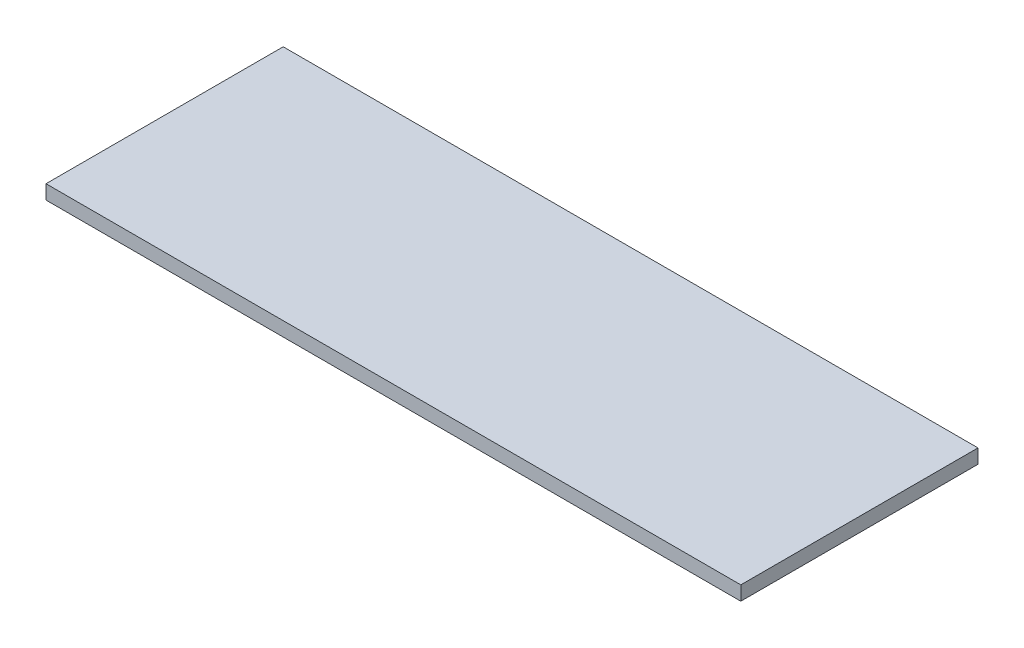
SolidWorks part; units mm, degrees
ref_plane "Front Plane" through (0, 0, 0) normal (0, 0, 1) x (1, 0, 0)
ref_plane "Top Plane" through (0, 0, 0) normal (0, 1, 0) x (1, 0, 0)
ref_plane "Right Plane" through (0, 0, 0) normal (1, 0, 0) x (0, 0, -1)
sketch "Sketch1" plane through (0, 0, 0) normal (0, 1, 0) x (1, 0, 0)
  line L1 (-930, 317.5) -> (930, 317.5)
  line L2 (-930, 317.5) -> (-930, -317.5)
  line L3 (-930, -317.5) -> (930, -317.5)
  line L4 (930, 317.5) -> (930, -317.5)
  line L5 (-930, 317.5) -> (930, -317.5) construction
  line L6 (-930, -317.5) -> (930, 317.5) construction
  point P0 (0, 0)
  dimension "D1" = 1860
  dimension "D2" = 635
extrude "Boss-Extrude1" add sketch "Sketch1" along normal blind 38
